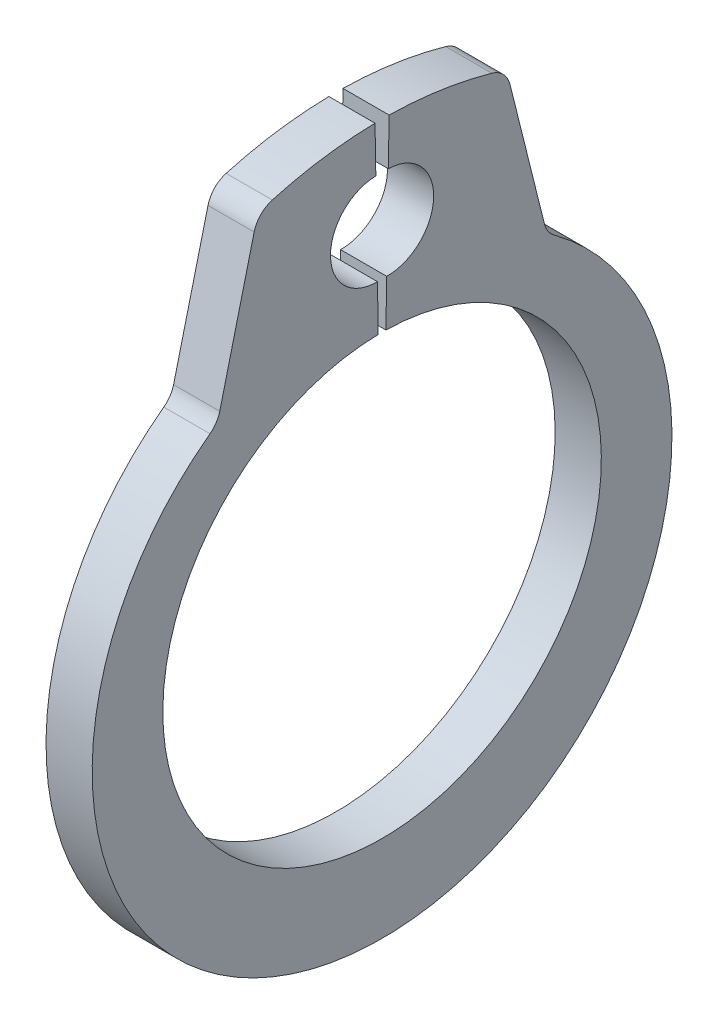
SolidWorks part; units mm, degrees
material "Cast Carbon Steel"
ref_plane "Front" through (0, 0, 0) normal (0, 0, 1) x (1, 0, 0)
ref_plane "Top" through (0, 0, 0) normal (0, 1, 0) x (1, 0, 0)
ref_plane "Right" through (0, 0, 0) normal (1, 0, 0) x (0, 0, -1)
sketch "Sketch1" plane through (0, 0, 0) normal (1, 0, 0) x (0, 0, -1)
  line L0 (0, 0) -> (0, 3.8) construction
  line L1 (-0.0663, 3.7994) -> (-0.1222, 6.9989) construction
  line L2 (-0.1222, 6.9989) -> (-2.0792, 6.9648) construction
  line L3 (-2.0792, 6.9648) -> (-2.8534, 3.8598) construction
  line L4 (0.1222, 6.9989) -> (0.0663, 3.7994) construction
  line L5 (0.1222, 6.9989) -> (2.0792, 6.9648) construction
  line L6 (2.0792, 6.9648) -> (2.8534, 3.8598) construction
  line L7 (-2.8534, 3.8598) -> (-2.2589, 3.0557) construction
  line L8 (2.8534, 3.8598) -> (2.2589, 3.0557) construction
  line L9 (0, -3.8) -> (0, -5.3) construction
  line L10 (-2.0792, 6.9648) -> (-0.0663, 3.7994) construction
  line L11 (0.0663, 3.7994) -> (0.0803, 4.5993)
  line L12 (0, 3.8) -> (0, 7) construction
  line L13 (2.1552, 6.66) -> (2.8534, 3.8598)
  line L14 (-2.1552, 6.66) -> (-2.8534, 3.8598)
  line L16 (0.1082, 6.1991) -> (0.1222, 6.9989)
  line L17 (-0.1082, 6.1991) -> (-0.1222, 6.9989)
  line L18 (-0.0803, 4.5993) -> (-0.0663, 3.7994)
  circle A0 centre (0, 0) radius 3.8 construction
  arc A1 (-0.0663, 3.7994) -> (0.0663, 3.7994) centre (0, 0) ccw
  circle A2 centre (0, -0.2757) radius 5.0243 construction
  arc A3 (0.1082, 6.1991) -> (0.0803, 4.5993) centre (0.0942, 5.3992) cw
  arc A4 (-0.0803, 4.5993) -> (-0.1082, 6.1991) centre (-0.0942, 5.3992) cw
  arc A6 (-2.8534, 3.8598) -> (2.8534, 3.8598) centre (0, -0.2757) ccw
  arc A7 (0.1222, 6.9989) -> (2.1552, 6.66) centre (0, 0) cw
  arc A8 (-0.1222, 6.9989) -> (-2.1552, 6.66) centre (0, 0) ccw
  dimension "D1" = 75
  dimension "A" = 7.6
  dimension "D2" = 1.6
  dimension "Smin" = 1
  dimension "Smax" = 1.5
  dimension "H" = 3.2
  dimension "Angle" = 1
extrude "Extrude1" add sketch "Sketch1" along normal mid plane 0.8
fillet "Fillet1" radius 0.45 4 edges at (0, 3.8598, 2.8534) (0, 6.66, 2.1552) (0, 6.66, -2.1552) (0, 3.8598, -2.8534)
sketch "Sketch2" plane through (0, 0, 0) normal (0, 0, 1) x (1, 0, 0)
  line L0 (-2.25, 0) -> (6.75, 0)
  line L1 (6.75, 0) -> (6.75, -4)
  line L2 (-0.45, -4) -> (-2.05, -4)
  line L3 (6.75, -4) -> (0.45, -4)
  line L4 (0.45, -4) -> (0.45, -3.8)
  line L5 (0.45, -3.8) -> (-0.45, -3.8)
  line L6 (-0.45, -3.8) -> (-0.45, -4)
  line L7 (-0.45, -4) -> (-2.25, -4) construction
  line L8 (-2.25, -4) -> (-2.25, 0) construction
  line L9 (0, -3.8) -> (0, 0) construction
  line L10 (6.75, 0) -> (14.0551, 0) construction
  line L11 (-2.05, -4) -> (-2.25, -3.8)
  line L12 (-2.25, -3.8) -> (-2.25, 0)
  dimension "D1" = 45
  dimension "Dg" = 7.6
  dimension "Ds" = 8
  dimension "D2" = 9
  dimension "W" = 0.9
  dimension "D3" = 2.25
revolve "Revolve1" [suppressed] add sketch "Sketch2" angle 360 about L10
equation "\"D2@Sketch2\" = \"W@Sketch2\"*10"
equation "\"D3@Sketch2\" = \"D2@Sketch2\"/4"
equation "\"Smin@Sketch1\" = \"Smax@Sketch1\"/1.5"
equation "\"D2@Sketch1\" = \"H@Sketch1\"/2"
